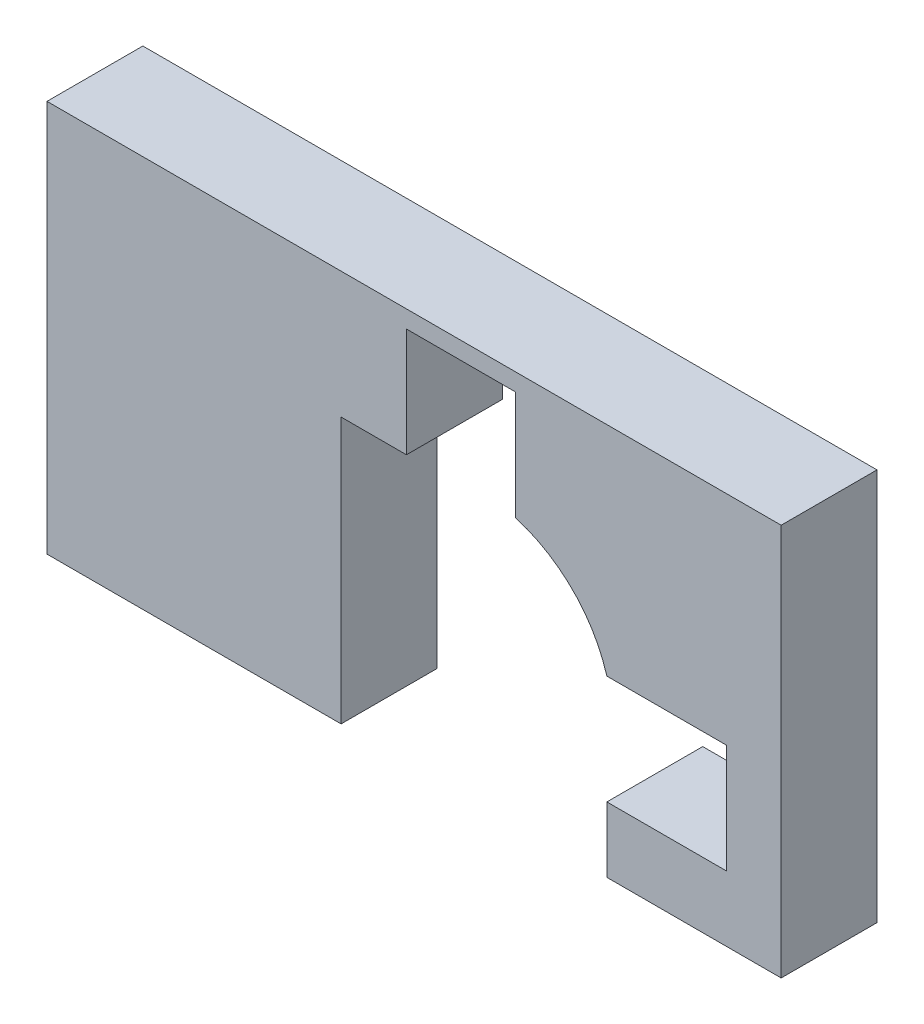
SolidWorks part; units mm, degrees
ref_plane "Front Plane" through (0, 0, 0) normal (0, 0, 1) x (1, 0, 0)
ref_plane "Top Plane" through (0, 0, 0) normal (0, 1, 0) x (1, 0, 0)
ref_plane "Right Plane" through (0, 0, 0) normal (1, 0, 0) x (0, 0, -1)
sketch "Sketch2" plane through (0, 0, 0) normal (0, 0, 1) x (1, 0, 0)
  line L6 (-62.5162, 80.614) -> (-32.5162, 80.614)
  line L7 (-197.5162, 138.614) -> (-197.5162, -41.386)
  line L10 (139.4838, 138.614) -> (139.4838, -41.386)
  line L12 (-62.5162, -41.386) -> (59.4838, -41.386) construction
  line L15 (-197.5162, 138.614) -> (139.4838, 138.614)
  line L16 (-62.5162, -41.386) -> (-62.5162, 80.614)
  line L19 (59.4838, -11.386) -> (59.4838, -41.386)
  line L22 (-32.5162, 130.614) -> (17.4838, 130.614)
  line L24 (59.4838, 38.614) -> (114.4838, 38.614)
  line L25 (114.4838, 38.614) -> (114.4838, -11.386)
  line L26 (114.4838, -11.386) -> (59.4838, -11.386)
  line L27 (-32.5162, 130.614) -> (-32.5162, 80.614)
  line L28 (17.4838, 130.614) -> (17.4838, 80.614)
  line L32 (-62.5162, -41.386) -> (-197.5162, -41.386)
  line L36 (59.4838, -41.386) -> (139.4838, -41.386)
  arc A1 (17.4838, 80.614) -> (59.4838, 38.614) centre (0, 21.1303) cw
  point P16 (59.4838, -11.386)
  dimension "D1" = 62
  dimension "D3" = 135
  dimension "D4" = 122
  dimension "D2" = 50
  dimension "D5" = 80
  dimension "D6" = 50
  dimension "D7" = 55
  dimension "D8" = 50
  dimension "D9" = 122
  dimension "D10" = 30
  dimension "D11" = 30
  dimension "D12" = 180
extrude "Boss-Extrude1" add sketch "Sketch2" along normal blind 44
